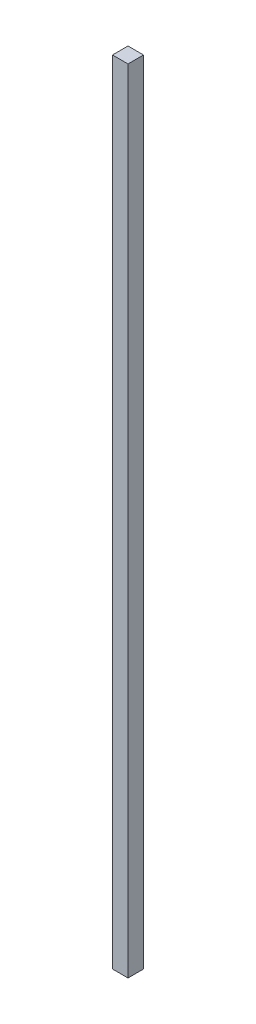
SolidWorks part; units mm, degrees
material "Custom Plastic"
ref_plane "Front Plane" through (0, 0, 0) normal (0, 0, 1) x (1, 0, 0)
ref_plane "Top Plane" through (0, 0, 0) normal (0, 1, 0) x (1, 0, 0)
ref_plane "Right Plane" through (0, 0, 0) normal (1, 0, 0) x (0, 0, -1)
sketch "Sketch1" plane through (0, 0, 0) normal (0, 1, 0) x (1, 0, 0)
  line L1 (-2.5, 2.5) -> (2.5, 2.5)
  line L2 (-2.5, 2.5) -> (-2.5, -2.5)
  line L3 (-2.5, -2.5) -> (2.5, -2.5)
  line L4 (2.5, 2.5) -> (2.5, -2.5)
  line L5 (-2.5, 2.5) -> (2.5, -2.5) construction
  line L6 (-2.5, -2.5) -> (2.5, 2.5) construction
  point P0 (0, 0)
extrude "Boss-Extrude1" add sketch "Sketch1" along normal blind 255
